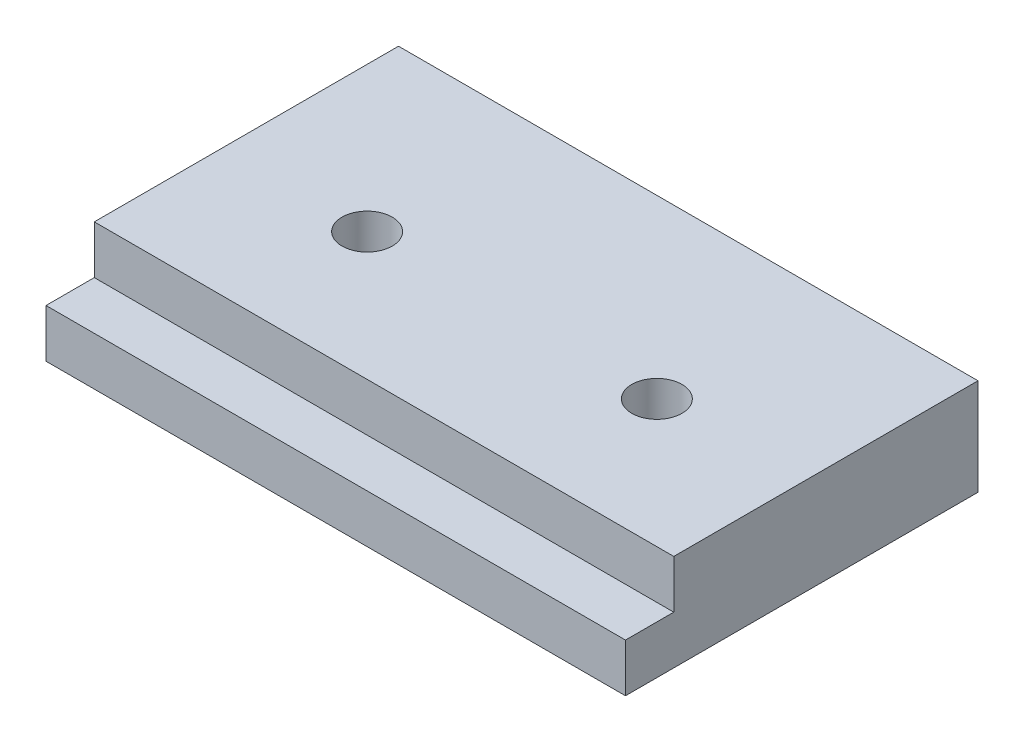
SolidWorks part; units mm, degrees
ref_plane "Front Plane" through (0, 0, 0) normal (0, 0, 1) x (1, 0, 0)
ref_plane "Top Plane" through (0, 0, 0) normal (0, 1, 0) x (1, 0, 0)
ref_plane "Right Plane" through (0, 0, 0) normal (1, 0, 0) x (0, 0, -1)
sketch "Sketch1" plane through (0, 0, 0) normal (0, 1, 0) x (1, 0, 0)
  line L1 (-30, -18.25) -> (30, -18.25)
  line L2 (-30, -18.25) -> (-30, 18.25)
  line L3 (-30, 18.25) -> (30, 18.25)
  line L4 (30, -18.25) -> (30, 18.25)
  line L5 (-30, -18.25) -> (30, 18.25) construction
  line L6 (-30, 18.25) -> (30, -18.25) construction
  point P0 (0, 0)
  dimension "D1" = 60
  dimension "D2" = 36.5
extrude "Boss-Extrude1" add sketch "Sketch1" along normal blind 10
sketch "Sketch2" plane through (0, 10, 0) normal (0, 1, 0) x (1, 0, 0)
  line L0 (30, -18.25) -> (30, 18.25) construction
  line L1 (-30, -18.25) -> (30, -18.25)
  line L2 (-30, -18.25) -> (-30, -13.25)
  line L3 (-30, -13.25) -> (30, -13.25)
  line L4 (30, -18.25) -> (30, -13.25)
  dimension "D1" = 5
extrude "Cut-Extrude1" cut sketch "Sketch2" against normal blind 5
sketch "Sketch3" plane through (0, 10, 0) normal (0, 1, 0) x (1, 0, 0)
  line L0 (0, 0) -> (0, -22.989) construction
  line L1 (0, 0) -> (-35.9589, 0) construction
  circle A0 centre (-15, 0) radius 3.8393
  circle A1 centre (15, 0) radius 3.8393
  dimension "D1" = 15
hole_wizard "Tap Drill for M5 Tap1" positions "3DSketch1" profile "Sketch4" hole size "M5" standard "GB"
sketch3d "3DSketch1"
  point P0 (-15, 10, 0)
  point P3 (15, 10, 0)
sketch "Sketch4" plane through (-15, 10, 0) normal (1, 0, 0) x (0, 0, 1)
  line L0 (0, 0) -> (0, 47.5622)
  line L1 (0, 47.5622) -> (2.6, 46)
  line L2 (2.6, 46) -> (2.6, 0)
  line L5 (2.6, 0) -> (0, 0)
  line L10 (0, 47.5622) -> (-2.6, 46) construction
  line L11 (0, -6.35) -> (0, 107.95) construction
  dimension "Hole Dia." = 5.2
  dimension "Hole Depth" = 46
  dimension "Drill Angle" = 118
